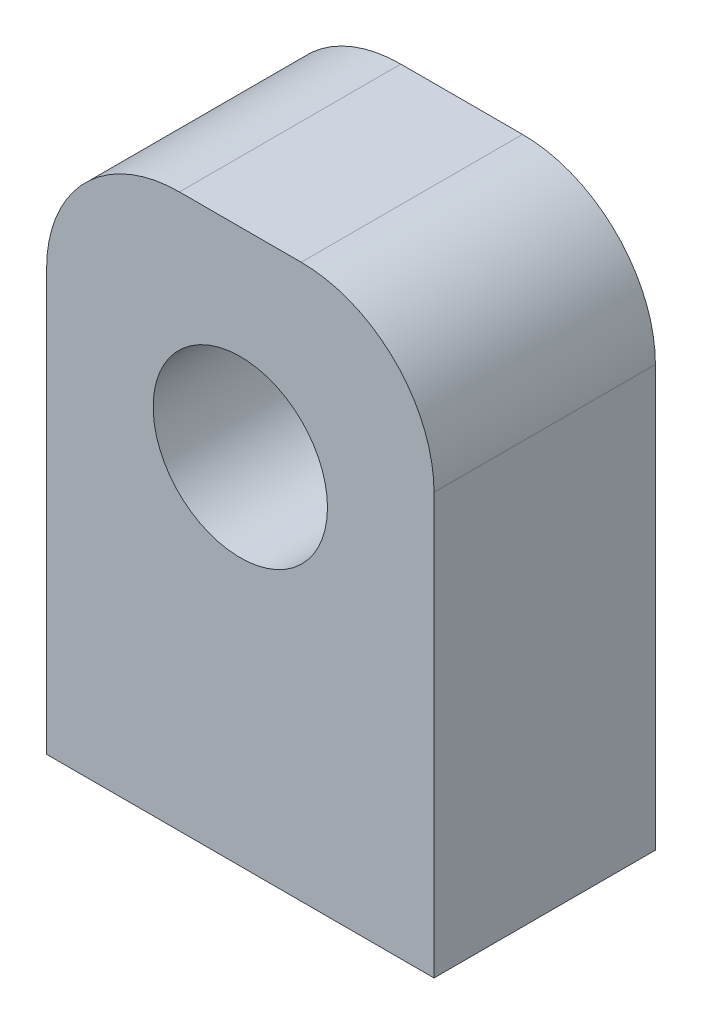
SolidWorks part; units mm, degrees
ref_plane "Front Plane" through (0, 0, 0) normal (0, 0, 1) x (1, 0, 0)
ref_plane "Top Plane" through (0, 0, 0) normal (0, 1, 0) x (1, 0, 0)
ref_plane "Right Plane" through (0, 0, 0) normal (1, 0, 0) x (0, 0, -1)
sketch "Sketch1" plane through (0, 0, 0) normal (0, 1, 0) x (1, 0, 0)
  line L1 (-16.3353, 9.1448) -> (18.6647, 9.1448)
  line L2 (-16.3353, 9.1448) -> (-16.3353, -10.8552)
  line L3 (-16.3353, -10.8552) -> (18.6647, -10.8552)
  line L4 (18.6647, 9.1448) -> (18.6647, -10.8552)
  dimension "D1" = 35
  dimension "D2" = 20
extrude "Boss-Extrude1" add sketch "Sketch1" along normal blind 50
sketch "Sketch2" plane through (0, 0, 10.8552) normal (0, 0, 1) x (1, 0, 0)
  line L0 (18.6647, 50) -> (18.6647, 0) construction
  line L1 (-16.3353, 0) -> (18.6647, 0) construction
  circle A0 centre (1.1647, 32) radius 7.875
  dimension "D1" = 17.5
  dimension "D2" = 32
extrude "Cut-Extrude1" cut sketch "Sketch2" against normal through all
sketch "Sketch3" plane through (0, 0, 0) normal (0, -1, 0) x (1, 0, 0)
  line L0 (18.6647, -9.1448) -> (-16.3353, -9.1448) construction
  line L1 (-16.3353, -9.1448) -> (-16.3353, 10.8552) construction
  line L2 (18.6647, 10.8552) -> (18.6647, -9.1448) construction
  circle A0 centre (-8.3353, 0.8552) radius 1.75
  circle A1 centre (10.6647, 0.8552) radius 1.75
  point P4 (-16.3353, 0.8552)
  dimension "D1" = 10
  dimension "D3" = 10
  dimension "D2" = 8
  dimension "D4" = 8
extrude "Cut-Extrude2" cut sketch "Sketch3" against normal blind 10
fillet "Fillet1" radius 12 2 edges at (18.6647, 50, 0.8552) (-16.3353, 50, 0.8552)
